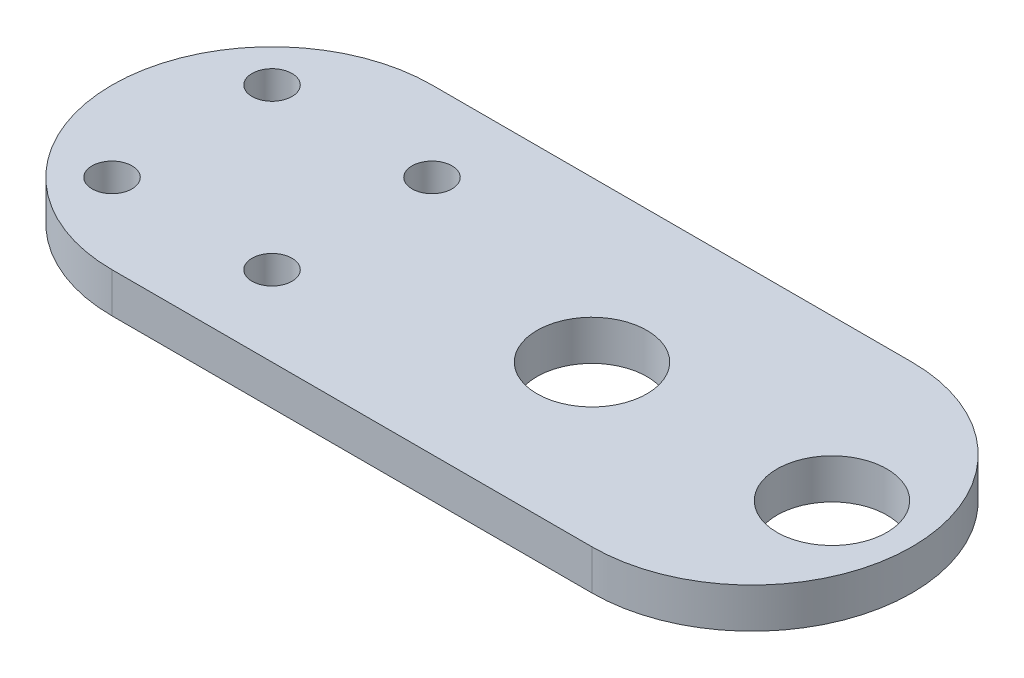
SolidWorks part; units mm, degrees
material "1060 Alloy"
ref_plane "Front Plane" through (0, 0, 0) normal (0, 0, 1) x (1, 0, 0)
ref_plane "Top Plane" through (0, 0, 0) normal (0, 1, 0) x (1, 0, 0)
ref_plane "Right Plane" through (0, 0, 0) normal (1, 0, 0) x (0, 0, -1)
sketch "Sketch1" plane through (0, 0, 0) normal (0, 1, 0) x (1, 0, 0)
  line L0 (12.7, 0) -> (12.7, 50.8) construction
  line L1 (25.4, 0) -> (101.6, 0)
  line L3 (25.4, 50.8) -> (101.6, 50.8)
  line L5 (25.4, 0) -> (25.4, 50.8) construction
  line L6 (12.7, 25.4) -> (25.4, 25.4) construction
  line L7 (12.7, 25.4) -> (0, 25.4) construction
  line L8 (25.4, 25.4) -> (127, 25.4) construction
  circle A0 centre (12.7, 38.1) radius 3.175
  circle A1 centre (38.1, 38.1) radius 3.175
  circle A2 centre (38.1, 12.7) radius 3.175
  circle A3 centre (12.7, 12.7) radius 3.175
  circle A4 centre (114.3, 25.4) radius 8.7262
  circle A5 centre (76.2, 25.4) radius 8.7262
  arc A6 (25.4, 50.8) -> (25.4, 0) centre (25.4, 25.4) ccw
  arc A8 (101.6, 0) -> (101.6, 50.8) centre (101.6, 25.4) ccw
  dimension "D5" = 6.35
  dimension "D7" = 17.4523
  dimension "D9" = 17.4523
  dimension "D2" = 50.8
  dimension "D3" = 50.8
  dimension "D1" = 38.1
  dimension "D4" = 12.7
  dimension "D6" = 12.7
extrude "Boss-Extrude1" add sketch "Sketch1" along normal blind 6.35
